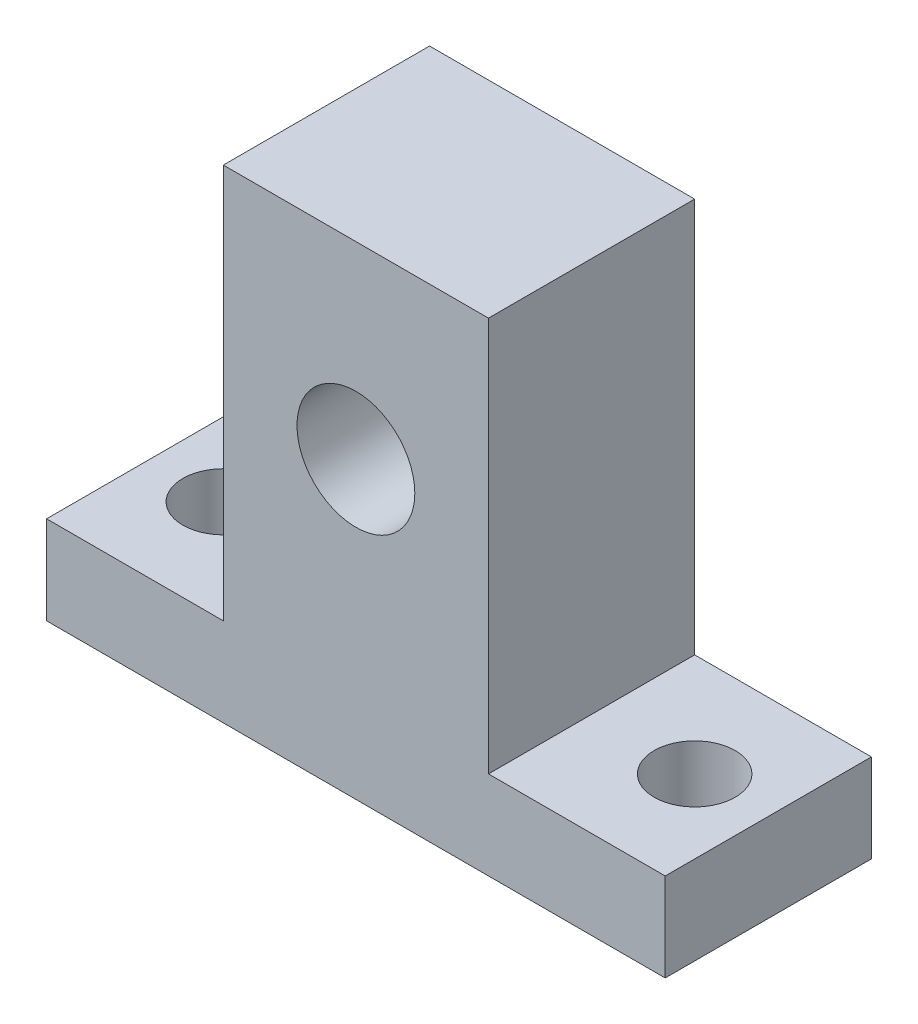
SolidWorks part; units mm, degrees
ref_plane "Front Plane" through (0, 0, 0) normal (0, 0, 1) x (1, 0, 0)
ref_plane "Top Plane" through (0, 0, 0) normal (0, 1, 0) x (1, 0, 0)
ref_plane "Right Plane" through (0, 0, 0) normal (1, 0, 0) x (0, 0, -1)
sketch "Sketch1" plane through (0, 0, 0) normal (0, 0, 1) x (1, 0, 0)
  line L0 (21, 0) -> (21, 65.2323) construction
  line L1 (0, 0) -> (42, 0)
  line L2 (0, 0) -> (0, 6)
  line L3 (0, 6) -> (12, 6)
  line L4 (42, 0) -> (42, 6)
  line L6 (12, 6) -> (12, 32.8)
  line L7 (12, 32.8) -> (30, 32.8)
  line L8 (30, 6) -> (30, 32.8)
  line L9 (30, 6) -> (42, 6)
  circle A0 centre (21, 20) radius 4
  dimension "D6" = 8
  dimension "D1" = 42
  dimension "D2" = 6
  dimension "D3" = 18
  dimension "D4" = 26.8
  dimension "D5" = 9
  dimension "D7" = 20
extrude "Boss-Extrude1" add sketch "Sketch1" along normal blind 14
sketch "Sketch2" plane through (0, 6, 0) normal (0, 1, 0) x (1, 0, 0)
  line L0 (0, -7) -> (42, -7) construction
  line L1 (0, -14) -> (0, 0) construction
  line L2 (42, -14) -> (42, 0) construction
  line L3 (21, -7) -> (21, 4.6113) construction
  circle A0 centre (5, -7) radius 2.75
  circle A1 centre (37, -7) radius 2.75
  dimension "D1" = 5.5
  dimension "D2" = 5.5
  dimension "D3" = 32
  dimension "D4" = 16
extrude "Cut-Extrude1" cut sketch "Sketch2" against normal through all
